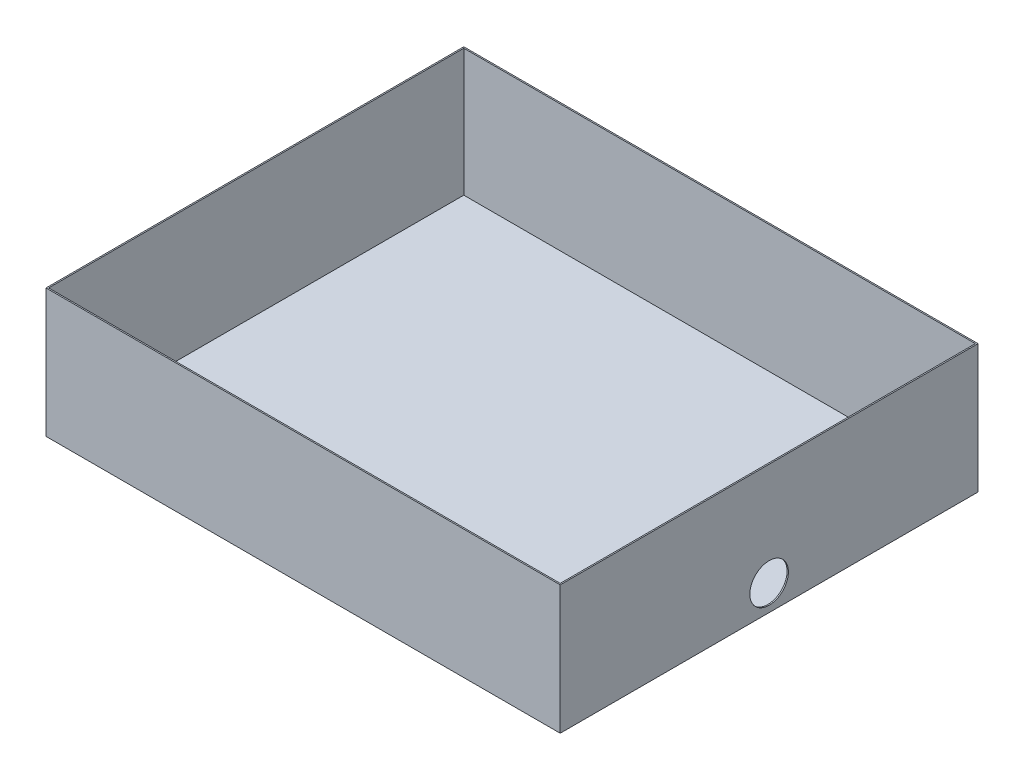
SolidWorks part; units mm, degrees
ref_plane "Front Plane" through (0, 0, 0) normal (0, 0, 1) x (1, 0, 0)
ref_plane "Top Plane" through (0, 0, 0) normal (0, 1, 0) x (1, 0, 0)
ref_plane "Right Plane" through (0, 0, 0) normal (1, 0, 0) x (0, 0, -1)
sketch "Sketch1" plane through (0, 0, 0) normal (0, 1, 0) x (1, 0, 0)
  line L1 (0, 0) -> (800, 0)
  line L2 (0, 0) -> (0, 650)
  line L3 (0, 650) -> (800, 650)
  line L4 (800, 0) -> (800, 650)
  dimension "D1" = 650
  dimension "80" = 800
extrude "Boss-Extrude1" add sketch "Sketch1" along normal blind 200
sketch "Sketch2" plane through (0, 200, 0) normal (0, 1, 0) x (1, 0, 0)
  line L0 (0, 650) -> (0, 0) construction
  line L1 (800, 650) -> (0, 650) construction
  line L2 (800, 0) -> (800, 650) construction
  line L3 (0, 0) -> (800, 0) construction
  line L6 (798, 2) -> (2, 2)
  line L7 (798, 2) -> (798, 648)
  line L8 (798, 648) -> (2, 648)
  line L9 (2, 2) -> (2, 648)
  dimension "D1" = 2
  dimension "D2" = 2
  dimension "D3" = 2
  dimension "D4" = 2
extrude "Cut-Extrude1" cut sketch "Sketch2" against normal blind 198
sketch "Sketch3" plane through (0, 0, 0) normal (-1, 0, 0) x (0, 0, 1)
  line L0 (0, 40) -> (-650, 40) construction
  line L1 (-650, 200) -> (-650, 0) construction
  line L2 (0, 200) -> (0, 0) construction
  line L3 (-650, 200) -> (0, 200) construction
  circle A0 centre (-325, 40) radius 30
  dimension "D1" = 60
  dimension "D2" = 160
sketch "Sketch4" plane through (800, 0, 0) normal (1, 0, 0) x (0, 0, -1)
  line L0 (0, 40) -> (650, 40) construction
  circle A0 centre (325, 40) radius 30
  dimension "D1" = 60
extrude "Cut-Extrude3" cut sketch "Sketch4" against normal up to next
